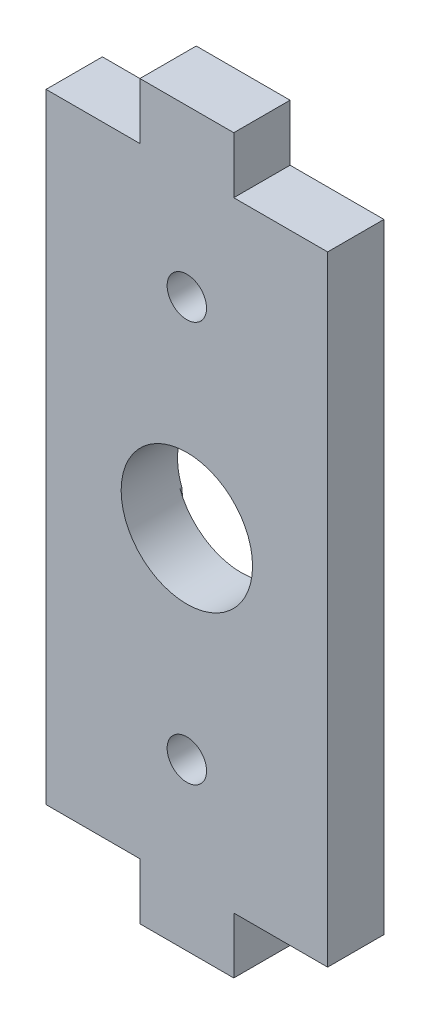
SolidWorks part; units mm, degrees
ref_plane "Alzado" through (0, 0, 0) normal (0, 0, 1) x (1, 0, 0)
ref_plane "Planta" through (0, 0, 0) normal (0, 1, 0) x (1, 0, 0)
ref_plane "Vista lateral" through (0, 0, 0) normal (1, 0, 0) x (0, 0, -1)
sketch "Corte exterior" plane through (0, 0, 0) normal (0, 0, 1) x (1, 0, 0)
  line L0 (28.7, -4.2) -> (23.7, -4.2)
  line L1 (18.7, 9.8) -> (18.7, -1.2)
  line L2 (18.7, 31.8) -> (18.7, 9.8)
  line L3 (23.7, 31.8) -> (18.7, 31.8)
  line L4 (23.7, 34.8) -> (23.7, 31.8)
  line L5 (28.7, 34.8) -> (23.7, 34.8)
  line L6 (28.7, 31.8) -> (28.7, 34.8)
  line L7 (33.7, 31.8) -> (28.7, 31.8)
  line L8 (33.7, 15.8) -> (33.7, 31.8)
  line L9 (23.7, -1.2) -> (23.7, -4.2)
  line L10 (18.7, -1.2) -> (23.7, -1.2)
  line L11 (33.7, -1.2) -> (33.7, 15.8)
  line L12 (28.7, -1.2) -> (33.7, -1.2)
  line L13 (28.7, -4.2) -> (28.7, -1.2)
  circle A0 centre (26.2, 25.9722) radius 1.05
  circle A1 centre (26.2, 4.6278) radius 1.05
  circle A2 centre (26.2, 15.3) radius 3.5
sketch "Grabado Superficie" plane through (0, 0, 0) normal (0, 0, 1) x (1, 0, 0)
  line L0 (22.9308, 16.55) -> (24.2, 29.3)
  line L1 (28.1903, 29.4966) -> (29.4692, 16.55)
  line L2 (29.4692, 14.05) -> (28.2, 1)
  line L3 (24.2, 1) -> (22.9308, 14.05)
  arc A0 (29.4692, 16.55) -> (22.9308, 16.55) centre (26.2, 15.3) ccw
  arc A1 (28.1903, 29.4966) -> (24.2, 29.3) centre (26.2, 29.3) ccw
  arc A2 (22.9308, 14.05) -> (29.4692, 14.05) centre (26.2, 15.3) ccw
  arc A3 (24.2, 1) -> (28.2, 1) centre (26.2, 1) ccw
extrude "Saliente-Extruir1" add sketch "Corte exterior" along normal blind 3
extrude "Cortar-Extruir1" cut sketch "Grabado Superficie" along normal blind 0.1
